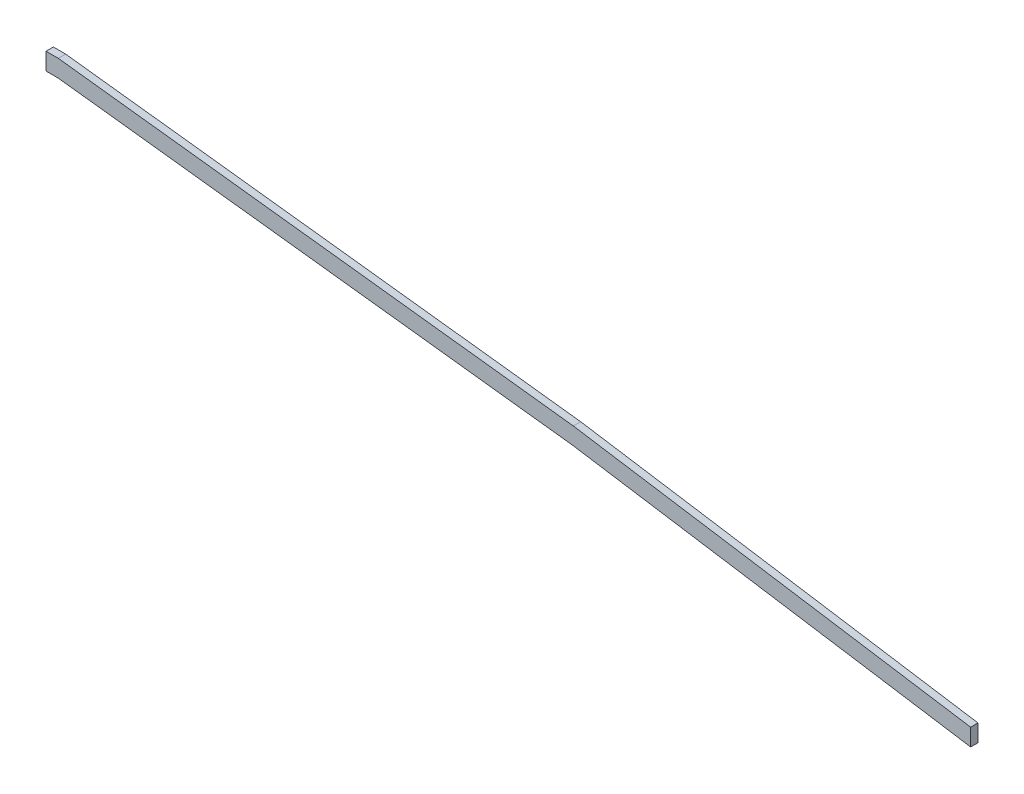
SolidWorks part; units mm, degrees
ref_plane "Front Plane" through (0, 0, 0) normal (0, 0, 1) x (1, 0, 0)
ref_plane "Top Plane" through (0, 0, 0) normal (0, 1, 0) x (1, 0, 0)
ref_plane "Right Plane" through (0, 0, 0) normal (1, 0, 0) x (0, 0, -1)
sketch "Sketch1" plane through (0, 0, 0) normal (0, 0, 1) x (1, 0, 0)
  line L0 (0, 0) -> (0, -7) construction
  line L1 (0, -7) -> (210, -31.818)
  line L2 (210, -31.818) -> (372, -57.1865)
  line L3 (372, -57.1865) -> (372, -50.1865)
  line L4 (372, -50.1865) -> (210, -24.818)
  line L5 (210, -24.818) -> (0, 0)
  line L7 (0, 0) -> (-5, 0)
  line L8 (0, 0) -> (0, -7) construction
  line L9 (0, -7) -> (-5, -7)
  line L10 (-5, 0) -> (-5, -7)
  point P3 (0, -6.8806)
  dimension "D1" = 83.26
  dimension "D2" = 177.84
  dimension "D3" = 372
  dimension "D4" = 210
  dimension "D5" = 7
  dimension "D6" = 7
  dimension "D7" = 7
  dimension "D8" = 5
extrude "Boss-Extrude1" add sketch "Sketch1" along normal blind 3
